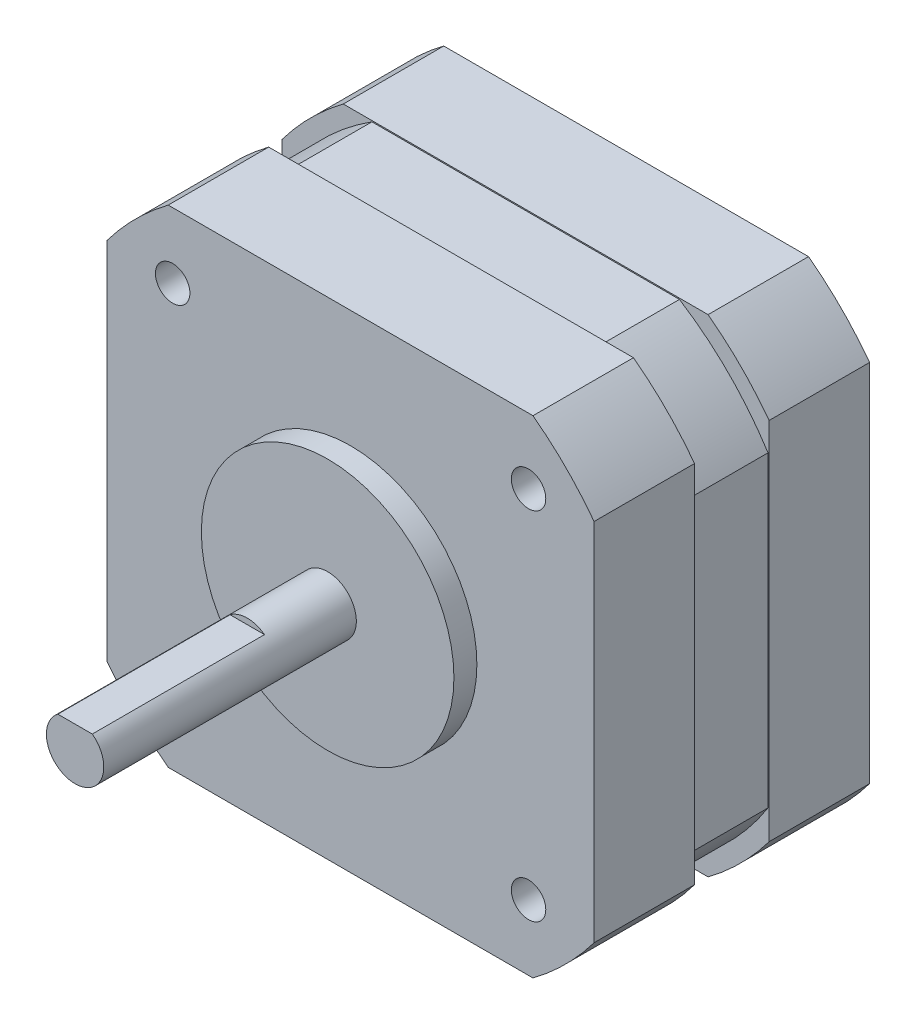
SolidWorks part; units mm, degrees
material "Plain Carbon Steel"
ref_plane "Front" through (0, 0, 0) normal (0, 0, 1) x (1, 0, 0)
ref_plane "Top" through (0, 0, 0) normal (0, 1, 0) x (1, 0, 0)
ref_plane "Right" through (0, 0, 0) normal (1, 0, 0) x (0, 0, -1)
sketch "Sketch1" plane through (0, 0, 0) normal (0, 0, 1) x (1, 0, 0)
  circle A0 centre (0, 0) radius 2.5
  dimension "D1" = 5
extrude "Boss-Extrude1" add sketch "Sketch1" along normal blind 24
sketch "Sketch2" plane through (0, 0, 0) normal (0, 0, -1) x (-1, 0, 0)
  circle A0 centre (0, 0) radius 11
  dimension "D1" = 22
extrude "Boss-Extrude2" add sketch "Sketch2" against normal blind 2
sketch "Sketch3" plane through (0, 0, 0) normal (0, 0, -1) x (-1, 0, 0)
  line L1 (21.209, -21.209) -> (-21.209, -21.209)
  line L2 (21.209, -21.209) -> (21.209, 21.209)
  line L3 (21.209, 21.209) -> (-21.209, 21.209)
  line L4 (-21.209, -21.209) -> (-21.209, 21.209)
  line L5 (21.209, -21.209) -> (-21.209, 21.209) construction
  line L6 (21.209, 21.209) -> (-21.209, -21.209) construction
  point P0 (0, 0)
  dimension "D1" = 42.418
extrude "Boss-Extrude3" add sketch "Sketch3" along normal blind 24
sketch "Sketch4" plane through (0, 0, -24) normal (0, 0, -1) x (-1, 0, 0)
  line L0 (-21.209, -15.888) -> (-21.209, -21.209)
  line L1 (15.888, -21.209) -> (21.209, -21.209)
  line L2 (21.209, 15.888) -> (21.209, 21.209)
  line L3 (-15.888, 21.209) -> (-21.209, 21.209)
  line L4 (-21.209, 21.209) -> (-21.209, -21.209)
  line L5 (-21.209, -21.209) -> (21.209, -21.209)
  line L6 (21.209, -21.209) -> (21.209, 21.209)
  line L7 (21.209, 21.209) -> (-21.209, 21.209)
  line L8 (-21.209, 21.209) -> (-21.209, 15.888)
  line L9 (-21.209, -21.209) -> (-15.888, -21.209)
  line L10 (21.209, -21.209) -> (21.209, -15.888)
  line L11 (21.209, 21.209) -> (15.888, 21.209)
  arc A0 (-21.209, -15.888) -> (-15.888, -21.209) centre (0, 0) ccw
  arc A1 (15.888, -21.209) -> (21.209, -15.888) centre (0, 0) ccw
  arc A2 (21.209, 15.888) -> (15.888, 21.209) centre (0, 0) ccw
  arc A3 (-15.888, 21.209) -> (-21.209, 15.888) centre (0, 0) ccw
  dimension "D2" = 26.5
  dimension "D1" = 0
extrude "Cut-Extrude1" cut sketch "Sketch4" against normal through all
hole_wizard "M3x0.5 Tapped Hole1" positions "Sketch6" profile "Sketch5" tap size "M3x0.5" standard "ANSI Metric"
sketch "Sketch6" plane through (0, 0, 0) normal (0, 0, 1) x (1, 0, 0)
  line L0 (-16.1632, 0) -> (0, 0) construction
  line L1 (0, 0) -> (0, 15.0764) construction
  point P0 (-15.5, 15.5)
  point P11 (-15.5, -15.5)
  point P12 (15.5, -15.5)
  point P13 (15.5, 15.5)
  dimension "D1" = 31
  dimension "D2" = 31
sketch "Sketch5" plane through (-15.5, 15.5, 0) normal (1, 0, 0) x (0, -1, 0)
  line L0 (0, 0) -> (0, 8.2511)
  line L1 (0, 8.2511) -> (1.25, 7.5)
  line L2 (1.25, 7.5) -> (1.25, 6)
  line L3 (1.25, 6) -> (1.5, 6)
  line L4 (1.5, 6) -> (1.5, 0)
  line L5 (1.5, 0) -> (0, 0)
  line L10 (0, 8.2511) -> (-1.25, 7.5) construction
  line L11 (0, -6.35) -> (0, 107.95) construction
  dimension "Tap Drill Dia." = 2.5
  dimension "Tap Drill Depth" = 7.5
  dimension "Thread Major Dia." = 3
  dimension "Thread Depth" = 6
  dimension "Drill Angle" = 118
sketch "Sketch7" plane through (0, 0, 24) normal (0, 0, 1) x (1, 0, 0)
  line L0 (-1.5, 2) -> (1.5, 2)
  circle A0 centre (0, 0) radius 2.5 construction
  circle A1 centre (0, 0) radius 2.5 construction
  arc A2 (1.5, 2) -> (-1.5, 2) centre (0, 0) ccw
  dimension "D1" = 4.5
extrude "Cut-Extrude2" cut sketch "Sketch7" against normal blind 15
ref_plane "Plane1" through (0, 0, -12) normal (0, 0, 1) x (1, 0, 0)
sketch "Sketch8" plane through (0, 0, -12) normal (0, 0, 1) x (1, 0, 0)
  line L0 (-13.3944, 21.109) -> (13.3944, 21.109)
  line L1 (-5.7152, 0) -> (0, 0) construction
  line L2 (0, 0) -> (0, 8.4579) construction
  line L3 (-15.888, 21.209) -> (15.888, 21.209) construction
  line L4 (-13.3944, -21.109) -> (13.3944, -21.109)
  line L5 (-21.109, 13.3944) -> (-21.109, -13.3944)
  line L6 (-21.209, -15.888) -> (-21.209, 15.888) construction
  line L7 (21.109, 13.3944) -> (21.109, -13.3944)
  line L12 (15.888, 21.209) -> (-15.888, 21.209)
  line L13 (-21.209, 15.888) -> (-21.209, -15.888)
  line L14 (-15.888, -21.209) -> (15.888, -21.209)
  line L15 (21.209, -15.888) -> (21.209, 15.888)
  line L16 (15.888, 21.209) -> (-15.888, 21.209)
  line L17 (-21.209, 15.888) -> (-21.209, -15.888)
  line L18 (-15.888, -21.209) -> (15.888, -21.209)
  line L19 (21.209, -15.888) -> (21.209, 15.888)
  arc A0 (-13.3944, 21.109) -> (-21.109, 13.3944) centre (0, 0) ccw
  arc A1 (-21.109, -13.3944) -> (-13.3944, -21.109) centre (0, 0) ccw
  arc A2 (21.109, 13.3944) -> (13.3944, 21.109) centre (0, 0) ccw
  arc A3 (13.3944, -21.109) -> (21.109, -13.3944) centre (0, 0) ccw
  arc A5 (-15.888, 21.209) -> (-21.209, 15.888) centre (0, 0) ccw
  arc A6 (-21.209, -15.888) -> (-15.888, -21.209) centre (0, 0) ccw
  arc A7 (15.888, -21.209) -> (21.209, -15.888) centre (0, 0) ccw
  arc A8 (21.209, 15.888) -> (15.888, 21.209) centre (0, 0) ccw
  arc A9 (-15.888, 21.209) -> (-21.209, 15.888) centre (0, 0) ccw
  arc A10 (-21.209, -15.888) -> (-15.888, -21.209) centre (0, 0) ccw
  arc A11 (15.888, -21.209) -> (21.209, -15.888) centre (0, 0) ccw
  arc A12 (21.209, 15.888) -> (15.888, 21.209) centre (0, 0) ccw
  dimension "D1" = 50
  dimension "D2" = 0.1
  dimension "D3" = 0.1
  dimension "D4" = 0
extrude "Cut-Extrude3" cut sketch "Sketch8" against normal offset from surface 8.75 and the other way offset from surface (3.25 mm away) 8.75 up to face at (0, 0, -24) other way up to face at (-14, 15.5, 0)
